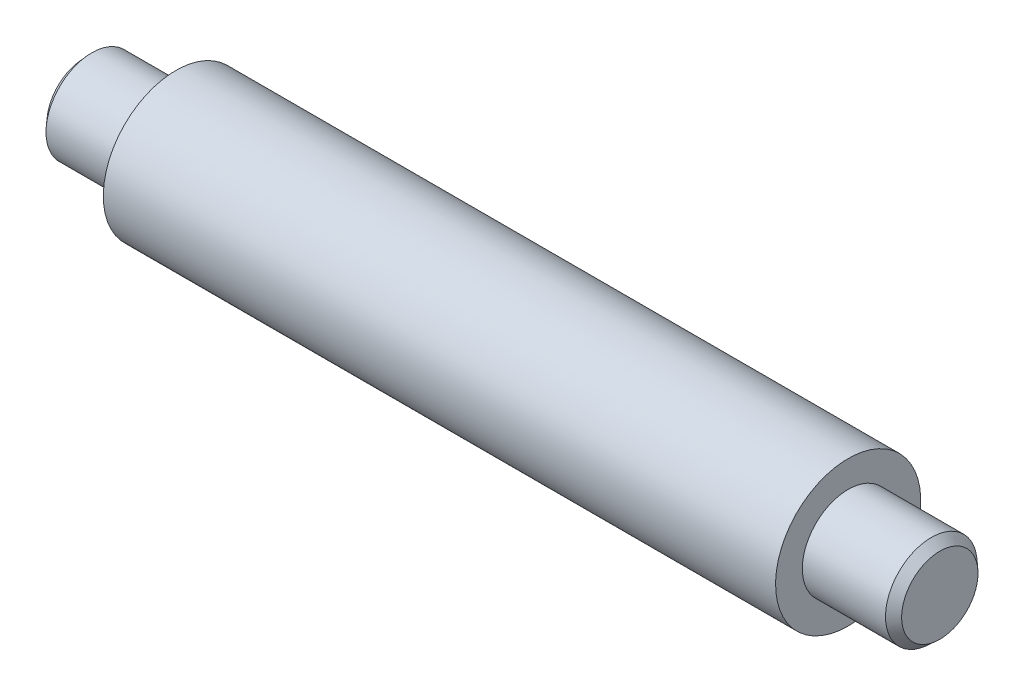
SolidWorks part; units mm, degrees
ref_plane "Ön Düzlem" through (0, 0, 0) normal (0, 0, 1) x (1, 0, 0)
ref_plane "Üst Düzlem" through (0, 0, 0) normal (0, 1, 0) x (1, 0, 0)
ref_plane "Sağ Düzlem" through (0, 0, 0) normal (1, 0, 0) x (0, 0, -1)
sketch "Çizim2" plane through (0, 0, 0) normal (0, 0, 1) x (1, 0, 0)
  line L0 (0, 30) -> (560, 30)
  line L1 (500, 60) -> (500, 77.5)
  line L2 (0, 30) -> (0, 60)
  line L3 (0, 60) -> (60, 60)
  line L6 (60, 60) -> (60, 77.5)
  line L7 (60, 77.5) -> (500, 77.5)
  line L11 (500, 60) -> (560, 60)
  line L12 (560, 30) -> (560, 60)
  dimension "D1" = 60
  dimension "D2" = 30
  dimension "D3" = 440
  dimension "D4" = 60
  dimension "D5" = 30
revolve "Döndür1" add sketch "Çizim2" angle 360 about L0
chamfer "Pah1" distance 5 angle 48 2 edges at (560, 0, 0) (0, 0, 0)
